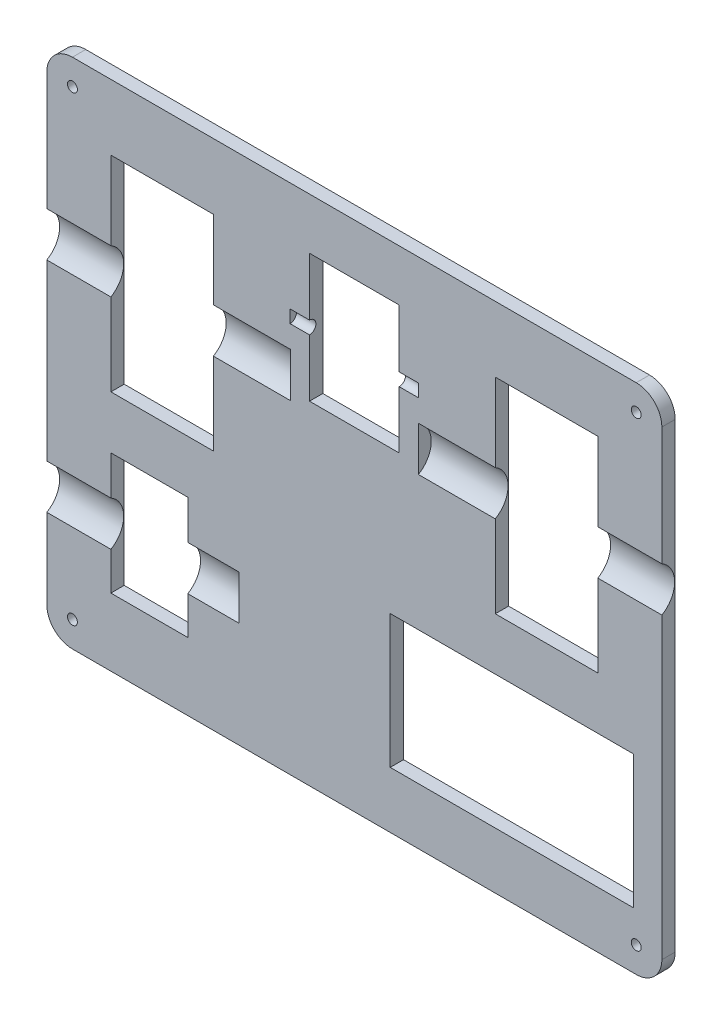
SolidWorks part; units mm, degrees
ref_plane "Front Plane" through (0, 0, 0) normal (0, 0, 1) x (1, 0, 0)
ref_plane "Top Plane" through (0, 0, 0) normal (0, 1, 0) x (1, 0, 0)
ref_plane "Right Plane" through (0, 0, 0) normal (1, 0, 0) x (0, 0, -1)
sketch "Sketch1" plane through (0, 0, 0) normal (0, 0, 1) x (1, 0, 0)
  line L1 (-152.4, 127) -> (152.4, 127)
  line L2 (-152.4, 127) -> (-152.4, -127)
  line L3 (-152.4, -127) -> (152.4, -127)
  line L4 (152.4, 127) -> (152.4, -127)
  dimension "D1" = 254
  dimension "D2" = 304.8
  dimension "D3" = 152.4
  dimension "D4" = 127
extrude "Boss-Extrude1" add sketch "Sketch1" along normal blind 6.604
fillet "Fillet1" radius 12.7 4 edges at (152.4, 127, 3.302) (152.4, -127, 3.302) (-152.4, -127, 3.302) (-152.4, 127, 3.302)
sketch "Sketch6" plane through (0, 0, 6.604) normal (0, 0, 1) x (1, 0, 0)
  line L0 (139.7, 127) -> (-139.7, 127) construction
  line L1 (-120.65, 94.488) -> (-69.85, 94.488)
  line L2 (-120.65, 94.488) -> (-120.65, -7.112)
  line L3 (-120.65, -7.112) -> (-69.85, -7.112)
  line L4 (-69.85, 94.488) -> (-69.85, -7.112)
  line L13 (-22.225, 101.6) -> (22.225, 101.6)
  line L14 (-22.225, 101.6) -> (-22.225, 38.1)
  line L15 (-22.225, 38.1) -> (22.225, 38.1)
  line L16 (22.225, 101.6) -> (22.225, 38.1)
  line L17 (-152.4, 114.3) -> (-152.4, -114.3) construction
  line L18 (-139.7, -127) -> (139.7, -127) construction
  line L19 (152.4, -114.3) -> (152.4, 114.3) construction
  line L20 (-120.65, -33.274) -> (-82.55, -33.274)
  line L21 (69.85, 94.488) -> (120.65, 94.488)
  line L22 (69.85, 94.488) -> (69.85, -7.112)
  line L23 (69.85, -7.112) -> (120.65, -7.112)
  line L24 (120.65, 94.488) -> (120.65, -7.112)
  line L25 (-120.65, -33.274) -> (-120.65, -93.472)
  line L26 (-120.65, -93.472) -> (-82.55, -93.472)
  line L27 (-82.55, -33.274) -> (-82.55, -93.472)
  line L28 (17.78, -33.02) -> (138.43, -33.02)
  line L29 (17.78, -33.02) -> (17.78, -99.06)
  line L30 (17.78, -99.06) -> (138.43, -99.06)
  line L31 (138.43, -33.02) -> (138.43, -99.06)
  dimension "D1" = 101.6
  dimension "D2" = 32.512
  dimension "D3" = 50.8
  dimension "D4" = 31.75
  dimension "D5" = 60.198
  dimension "D6" = 38.1
  dimension "D7" = 33.528
  dimension "D8" = 31.75
  dimension "D9" = 44.45
  dimension "D10" = 63.5
  dimension "D11" = 88.9
  dimension "D12" = 22.225
  dimension "D13" = 120.65
  dimension "D14" = 120.65
  dimension "D15" = 66.04
  dimension "D16" = 13.97
  dimension "D17" = 31.75
  dimension "D18" = 50.8
  dimension "D19" = 101.6
  dimension "D20" = 32.512
  dimension "D21" = 27.94
extrude "Cut-Extrude1" cut sketch "Sketch6" against normal blind 7.62
sketch "Sketch9" plane through (-152.4, 0, 0) normal (-1, 0, 0) x (0, 0, 1)
  line L2 (6.604, 55.626) -> (6.604, 33.629)
  line L3 (6.604, 114.3) -> (6.604, -114.3) construction
  arc A1 (6.604, 55.626) -> (6.604, 33.629) centre (12.954, 44.6275) ccw
  dimension "D3" = 25.4
  dimension "D4" = 6.35
  dimension "D1" = 40.741
extrude "Cut-Extrude2" cut sketch "Sketch9" against normal blind 120.65
mirror "Mirror1" about plane through (0, 0, 0) normal (1, 0, 0) of "Cut-Extrude2"
sketch "Sketch10" plane through (-152.4, 0, 0) normal (-1, 0, 0) x (0, 0, 1)
  line L1 (6.604, 33.629) -> (6.604, -114.3) construction
  line L2 (6.604, -52.679) -> (6.604, -74.676)
  arc A0 (6.604, -52.679) -> (6.604, -74.676) centre (12.954, -63.6775) ccw
  dimension "D1" = 25.4
  dimension "D2" = 6.35
  dimension "D3" = 52.324
extrude "Cut-Extrude3" cut sketch "Sketch10" against normal blind 95.25
sketch "Sketch11" plane through (22.225, 0, 0) normal (-1, 0, 0) x (0, 0, 1)
  line L0 (6.604, 38.1) -> (6.604, 101.6) construction
  line L1 (6.604, 72.898) -> (6.604, 66.548)
  arc A0 (6.604, 72.898) -> (6.604, 66.548) centre (6.604, 69.723) ccw
  dimension "D1" = 6.35
  dimension "D2" = 0
  dimension "D3" = 31.877
extrude "Cut-Extrude4" cut sketch "Sketch11" against normal blind 9.652
mirror "Mirror2" about plane through (0, 0, 0) normal (1, 0, 0) of "Cut-Extrude4"
hole_wizard "CSK for #8 Flat Head Machine Screw (100)1" positions "Sketch14" profile "Sketch15" countersink size "#8" standard "ANSI Inch"
sketch "Sketch14" plane through (0, 0, 0) normal (0, 0, -1) x (-1, 0, 0)
  line L0 (-152.4, -114.3) -> (-152.4, 114.3) construction
  line L1 (-139.7, 127) -> (139.7, 127) construction
  line L2 (152.4, 114.3) -> (152.4, -114.3) construction
  line L3 (139.7, -127) -> (-139.7, -127) construction
  point P0 (-139.7, 114.3)
  point P2 (139.7, 114.3)
  point P4 (139.7, -114.3)
  point P6 (-139.7, -114.3)
  dimension "D1" = 12.7
  dimension "D2" = 12.7
  dimension "D3" = 12.7
  dimension "D4" = 12.7
  dimension "D5" = 12.7
  dimension "D6" = 12.7
  dimension "D7" = 12.7
  dimension "D8" = 12.7
sketch "Sketch15" plane through (139.7, 114.3, 0) normal (1, 0, 0) x (0, 1, 0)
  line L0 (0, 0) -> (0, 12.1446)
  line L1 (0, 12.1446) -> (2.4574, 10.668)
  line L2 (2.4574, 10.668) -> (2.4574, 1.4759)
  line L3 (2.4574, 1.4759) -> (4.2164, 0)
  line L5 (4.2164, 0) -> (0, 0)
  line L6 (-2.4574, 1.4759) -> (-4.2164, 0) construction
  line L10 (0, 12.1446) -> (-2.4574, 10.668) construction
  line L11 (0, -6.35) -> (0, 107.95) construction
  dimension "Hole Dia." = 4.9149
  dimension "Hole Depth" = 10.668
  dimension "Near C'Sink Dia." = 8.4328
  dimension "Near C'Sink Angle" = 100
  dimension "Drill Angle" = 118
